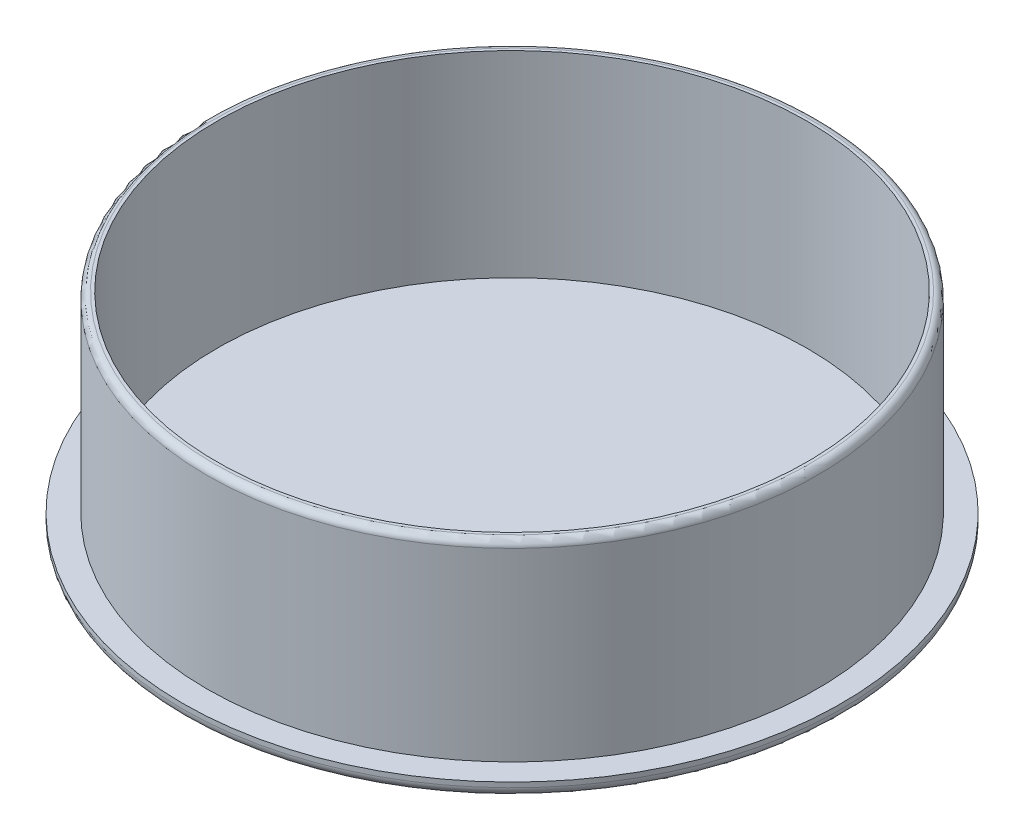
SolidWorks part; units mm, degrees
ref_plane "Ön Düzlem" through (0, 0, 0) normal (0, 0, 1) x (1, 0, 0)
ref_plane "Üst Düzlem" through (0, 0, 0) normal (0, 1, 0) x (1, 0, 0)
ref_plane "Sağ Düzlem" through (0, 0, 0) normal (1, 0, 0) x (0, 0, -1)
sketch "Sketch1" plane through (0, 0, 0) normal (0, 1, 0) x (1, 0, 0)
  circle A0 centre (0, 0) radius 62
extrude "Boss-Extrude1" add sketch "Sketch1" along normal blind 42
sketch "Sketch2" plane through (0, 0, 0) normal (0, 1, 0) x (1, 0, 0)
  circle A0 centre (0, 0) radius 67
extrude "Boss-Extrude2" add sketch "Sketch2" along normal blind 3
fillet "Fillet1" radius 2 1 edges at (0, 0, 67)
shell "Shell1" thickness 2
fillet "Fillet2" radius 1.4 1 edges at (0, 42, 62)
